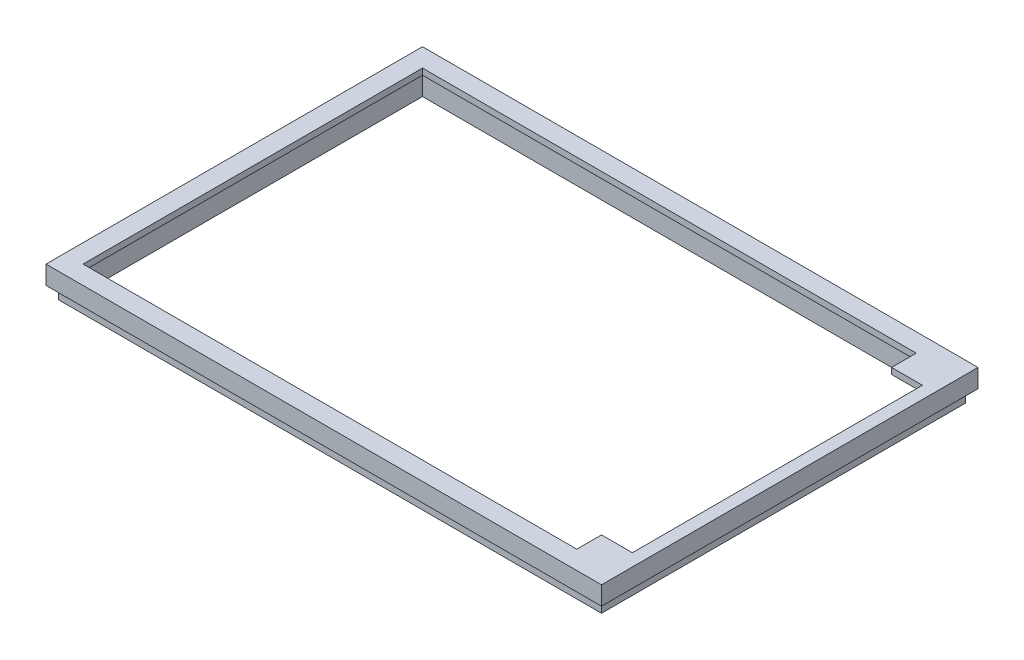
SolidWorks part; units mm, degrees
ref_plane "Front Plane" through (0, 0, 0) normal (0, 0, 1) x (1, 0, 0)
ref_plane "Top Plane" through (0, 0, 0) normal (0, 1, 0) x (1, 0, 0)
ref_plane "Right Plane" through (0, 0, 0) normal (1, 0, 0) x (0, 0, -1)
sketch "Sketch1" plane through (0, 0, 0) normal (0, 1, 0) x (1, 0, 0)
  line L0 (0, 0) -> (90, 0)
  line L1 (90, 0) -> (90, 61)
  line L2 (90, 61) -> (0, 61)
  line L3 (0, 61) -> (0, 0)
  line L4 (88, 59) -> (2, 59)
  line L5 (2, 59) -> (2, 2)
  line L6 (2, 2) -> (88, 2)
  line L7 (88, 2) -> (88, 59)
  dimension "D1" = 90
  dimension "D2" = 61
  dimension "D3" = 2
extrude "Boss-Extrude1" add sketch "Sketch1" along normal blind 3
sketch "Sketch2" plane through (0, 3, 0) normal (0, 1, 0) x (1, 0, 0)
  line L0 (88, 59) -> (83, 59)
  line L1 (88, 59) -> (2, 59) construction
  line L2 (83, 58) -> (83, 54)
  line L3 (83, 54) -> (88, 54)
  line L4 (88, 2) -> (88, 59) construction
  line L5 (88, 54) -> (88, 59)
  line L6 (0, 30.5) -> (22.2421, 30.5) construction
  line L7 (0, 61) -> (0, 0) construction
  line L8 (88, 2) -> (83, 2)
  line L9 (88, 7) -> (88, 2)
  line L10 (83, 3) -> (83, 7)
  line L11 (83, 7) -> (88, 7)
  line L12 (2, 59) -> (3, 59)
  line L13 (3, 58) -> (3, 3)
  line L14 (2, 2) -> (88, 2) construction
  line L15 (3, 2) -> (2, 2)
  line L16 (2, 2) -> (2, 59)
  line L17 (3, 58) -> (83, 58)
  line L19 (3, 59) -> (83, 59)
  line L20 (3, 2) -> (83, 2)
  line L21 (3, 3) -> (83, 3)
  dimension "D1" = 5
  dimension "D2" = 5
  dimension "D3" = 1
  dimension "D4" = 1
extrude "Boss-Extrude2" add sketch "Sketch2" against normal blind 1
sketch "Sketch3" plane through (0, 0, 0) normal (0, -1, 0) x (1, 0, 0)
  line L0 (2, -2) -> (88, -2) construction
  line L1 (2, -59) -> (2, -2) construction
  line L2 (88, -59) -> (2, -59) construction
  line L3 (88, -2) -> (88, -59) construction
  line L4 (2, -2) -> (88, -2)
  line L5 (2, -59) -> (2, -2)
  line L6 (88, -59) -> (2, -59)
  line L7 (88, -2) -> (88, -59)
  line L8 (1, -1) -> (89, -1)
  line L9 (89, -1) -> (89, -60)
  line L10 (89, -60) -> (1, -60)
  line L11 (1, -60) -> (1, -1)
  dimension "D1" = 1
extrude "Boss-Extrude3" add sketch "Sketch3" along normal blind 2
